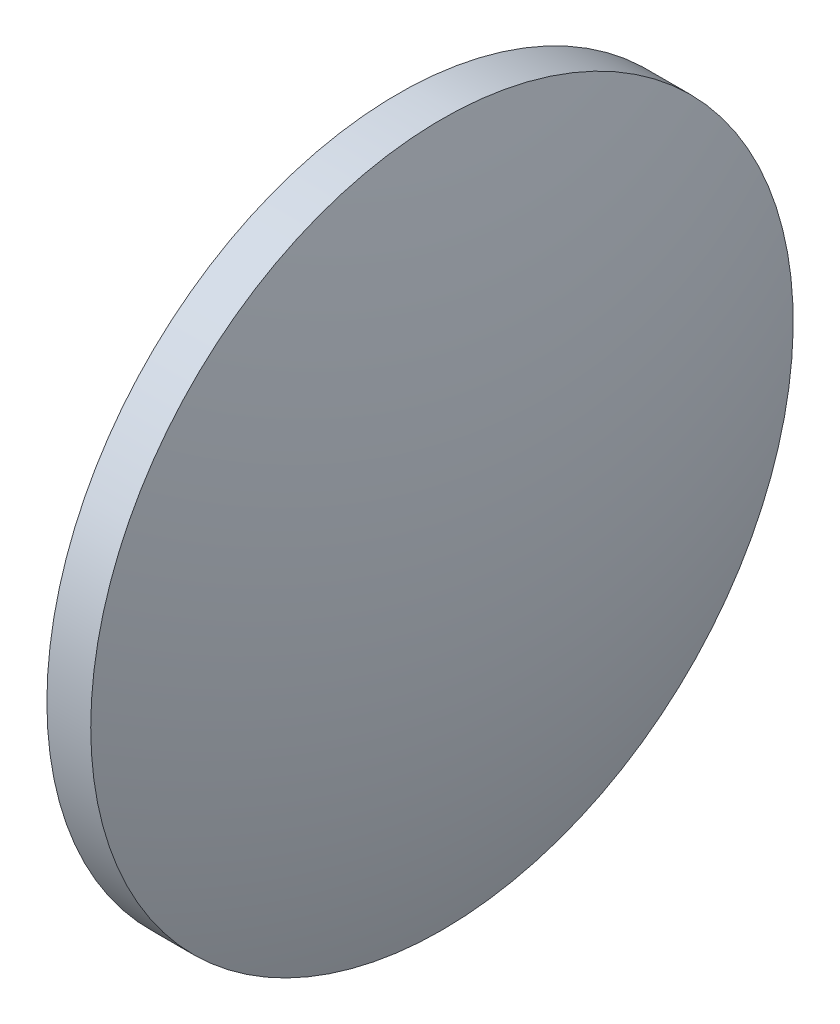
SolidWorks part; units mm, degrees
ref_plane "前视基准面" through (0, 0, 0) normal (0, 0, 1) x (1, 0, 0)
ref_plane "上视基准面" through (0, 0, 0) normal (0, 1, 0) x (1, 0, 0)
ref_plane "右视基准面" through (0, 0, 0) normal (1, 0, 0) x (0, 0, -1)
sketch "草图2" plane through (0, 0, 0) normal (0, 0, 1) x (1, 0, 0)
  line L0 (677.0001, 248.699) -> (730.7831, 248.699) construction
  line L1 (700.6482, 248.699) -> (700.6482, 261.199)
  line L2 (704.2482, 248.699) -> (700.6482, 248.699)
  line L5 (700.6482, 261.199) -> (702.2082, 261.199)
  arc A0 (704.2482, 248.699) -> (702.2082, 261.199) centre (664.9316, 248.699) ccw
revolve "旋转2" add sketch "草图2" angle 360 about L0
